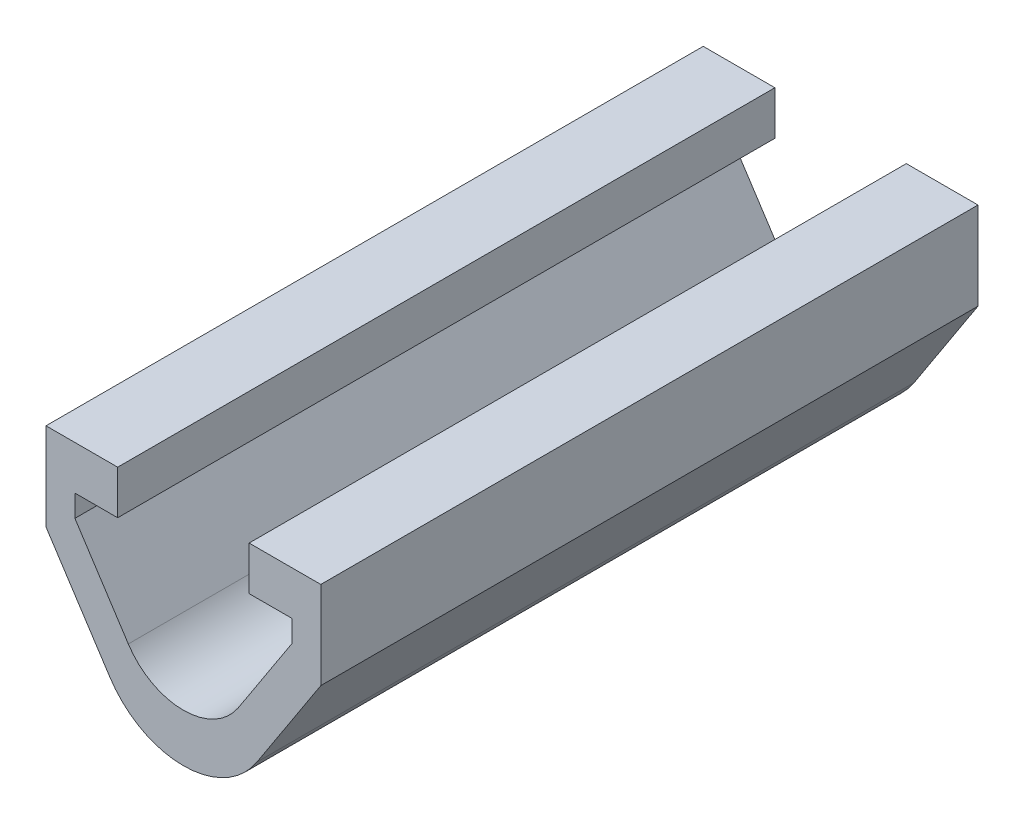
SolidWorks part; units mm, degrees
material "Maple"
ref_plane "Wasteboard" through (0, 0, 0) normal (0, 0, 1) x (1, 0, 0)
ref_plane "Left-Right" through (0, 0, 0) normal (0, 1, 0) x (1, 0, 0)
ref_plane "Front-Back" through (0, 0, 0) normal (1, 0, 0) x (0, 0, -1)
sketch "Sketch1" plane through (0, 0, 0) normal (0, 0, 1) x (1, 0, 0)
  line L0 (0, 7.7857) -> (0, -1.1667) construction
  line L1 (-3, -8.5) -> (3, -8.5) construction
  line L2 (3, -8.5) -> (4.9524, -5.5)
  line L3 (4.9524, -4.5) -> (3, -4.5)
  line L4 (3, -4.5) -> (3, -2.5)
  line L5 (3, -2.5) -> (6.2718, -2.5)
  line L8 (4.9524, -5.5) -> (4.9524, -4.5)
  line L9 (-4.9524, -5.5) -> (-4.9524, -4.5)
  line L10 (-6.2718, -2.5) -> (-6.2718, -6.5)
  line L11 (-3, -2.5) -> (-6.2718, -2.5)
  line L12 (-3, -4.5) -> (-3, -2.5)
  line L13 (-4.9524, -4.5) -> (-3, -4.5)
  line L14 (-3, -8.5) -> (-4.9524, -5.5)
  line L18 (0, -8.5) -> (0, -15.1898) construction
  line L19 (-3, -8.5) -> (-2.5144, -9.2461)
  line L20 (2.5144, -9.2461) -> (3, -8.5)
  line L21 (-6.2718, -6.5) -> (-3.3526, -10.9856)
  line L22 (3.3526, -10.9856) -> (6.2718, -6.5)
  line L23 (6.2718, -2.5) -> (6.2718, -6.5)
  arc A0 (-2.5144, -9.2461) -> (2.5144, -9.2461) centre (0, -7.6098) ccw
  arc A1 (-3.3526, -10.9856) -> (3.3526, -10.9856) centre (0, -8.8038) ccw
  point P19 (0, -8.5)
  point P22 (0, 0)
  point P25 (0, -16.6279)
  point P26 (0, 0)
  dimension "D6" = 3
  dimension "D8" = 4
  dimension "D1" = 6
  dimension "D2" = 2
  dimension "D3" = 3
  dimension "D4" = 1
  dimension "D5" = 6
  dimension "D7" = 4
extrude "Boss-Extrude2" add sketch "Sketch1" along normal blind 30 contours L21 A1 L22 L23 L5 L4 L3 L8 L2 L20 A0 L19 L14 L9 L13 L12 L11 L10
